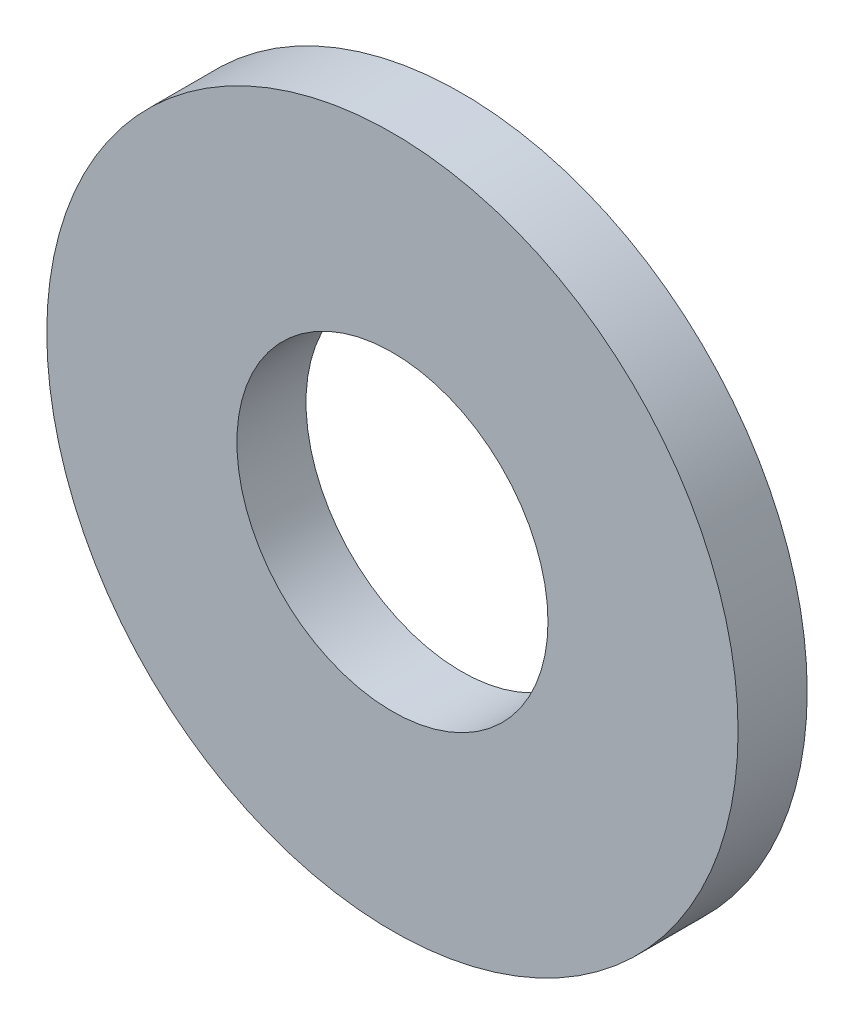
SolidWorks part; units mm, degrees
ref_plane "Front Plane" through (0, 0, 0) normal (0, 0, 1) x (1, 0, 0)
ref_plane "Top Plane" through (0, 0, 0) normal (0, 1, 0) x (1, 0, 0)
ref_plane "Right Plane" through (0, 0, 0) normal (1, 0, 0) x (0, 0, -1)
sketch "Sketch1" plane through (0, 0, 0) normal (0, 0, 1) x (1, 0, 0)
  circle A0 centre (0, 0) radius 7.9375
  circle A1 centre (0, 0) radius 3.5719
  dimension "D1" = 15.875
  dimension "D2" = 7.1437
extrude "Boss-Extrude1" add sketch "Sketch1" along normal blind 1.5875
